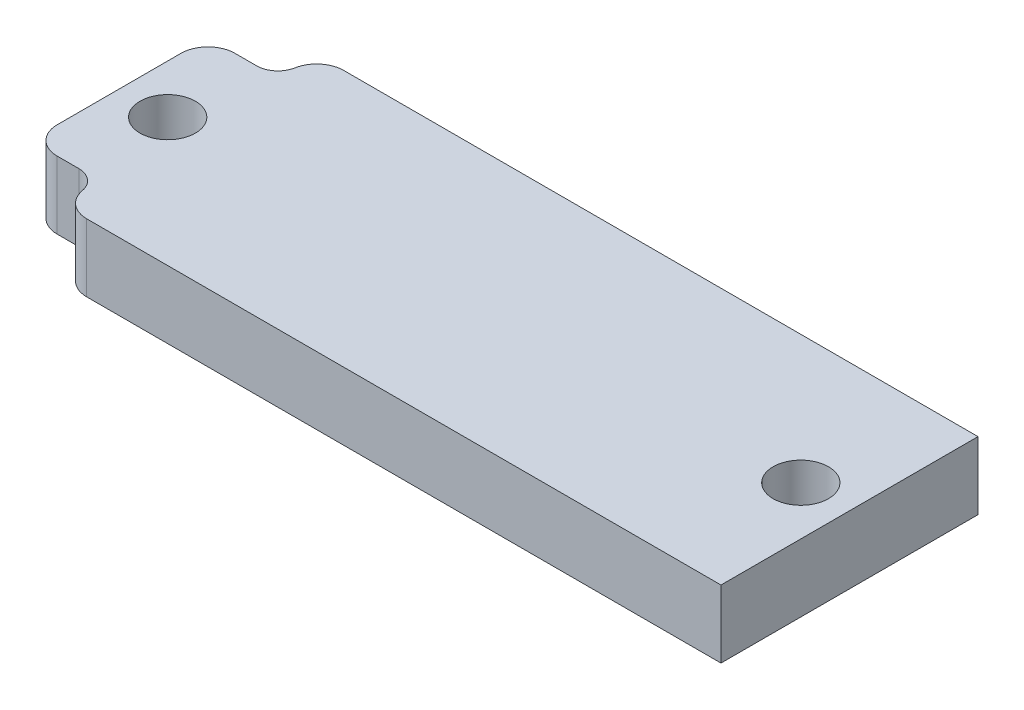
SolidWorks part; units mm, degrees
ref_plane "Front Plane" through (0, 0, 0) normal (0, 0, 1) x (1, 0, 0)
ref_plane "Top Plane" through (0, 0, 0) normal (0, 1, 0) x (1, 0, 0)
ref_plane "Right Plane" through (0, 0, 0) normal (1, 0, 0) x (0, 0, -1)
sketch "Sketch2" plane through (0, 0, 0) normal (0, 1, 0) x (1, 0, 0)
  line L1 (0, 0) -> (68.58, 0)
  line L2 (0, 0) -> (0, 24.13)
  line L3 (0, 24.13) -> (68.58, 24.13)
  line L4 (68.58, 0) -> (68.58, 24.13)
  circle A0 centre (4.57, 12.065) radius 2.6
  circle A1 centre (64.01, 12.065) radius 2.6
  point P10 (68.58, 12.065)
  dimension "D4" = 5.2
  dimension "D1" = 68.58
  dimension "D2" = 24.13
  dimension "D3" = 4.57
  dimension "D5" = 4.57
extrude "Boss-Extrude1" add sketch "Sketch2" along normal blind 6.35
sketch "Sketch3" plane through (0, 6.35, 0) normal (0, 1, 0) x (1, 0, 0)
  line L0 (6.57, 22.415) -> (6.57, 24.13)
  line L2 (4.57, 20.415) -> (0, 20.415)
  line L3 (0, 24.13) -> (0, 0) construction
  line L4 (68.58, 24.13) -> (0, 24.13) construction
  line L5 (4.57, 12.065) -> (64.01, 12.065) construction
  line L6 (34.29, 24.13) -> (34.29, 0) construction
  line L7 (0, 0) -> (68.58, 0) construction
  line L8 (6.57, 1.715) -> (6.57, 0)
  line L9 (4.57, 3.715) -> (0, 3.715)
  arc A0 (4.57, 20.415) -> (6.57, 22.415) centre (4.57, 22.415) ccw
  circle A1 centre (4.57, 12.065) radius 2.6 construction
  circle A2 centre (4.57, 12.065) radius 2.6
  arc A3 (4.57, 3.715) -> (6.57, 1.715) centre (4.57, 1.715) cw
  line M1 (0, 0) -> (68.58, 0)
  line M5 (68.58, 24.13) -> (0, 24.13)
  line M7 (0, 24.13) -> (0, 0)
  dimension "D1" = 10.35
  dimension "D2" = 4
extrude "Cut-Extrude1" cut sketch "Sketch3" against normal through all contours A3 L9 L8 M7 M1 | L2 A0 L0 M5 M7
fillet "Fillet3" radius 2.54 4 edges at (6.57, 3.175, 0) (0, 3.175, -3.715) (0, 3.175, -20.415) (6.57, 3.175, -24.13)
